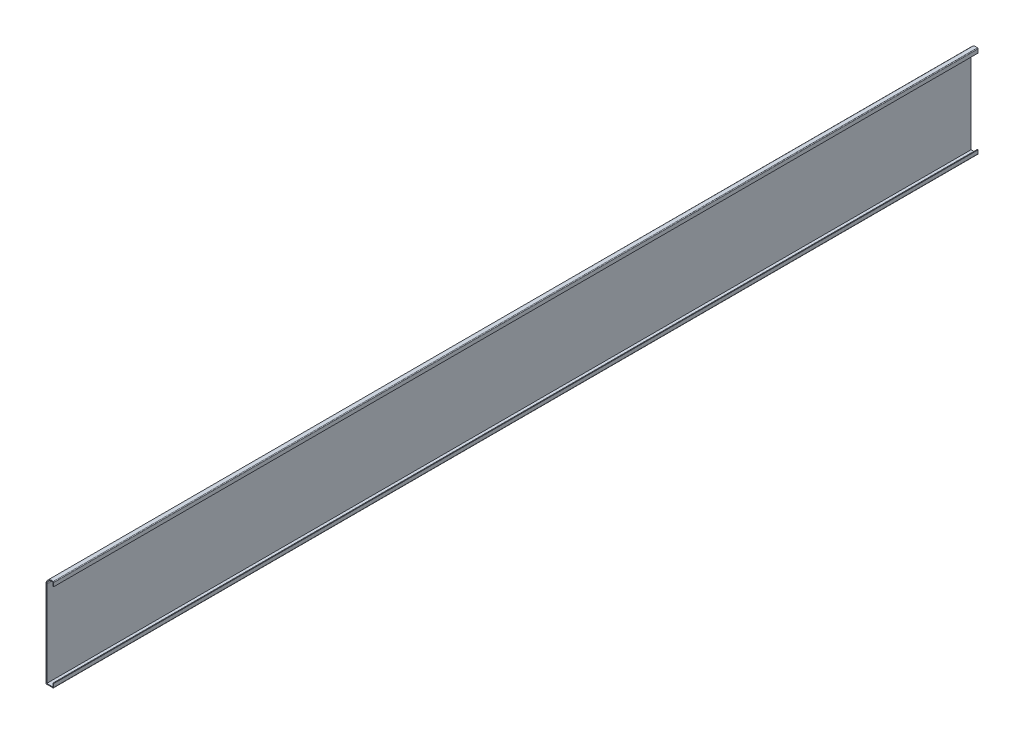
SolidWorks part; units mm, degrees
ref_plane "Front Plane" through (0, 0, 0) normal (0, 0, 1) x (1, 0, 0)
ref_plane "Top Plane" through (0, 0, 0) normal (0, 1, 0) x (1, 0, 0)
ref_plane "Right Plane" through (0, 0, 0) normal (1, 0, 0) x (0, 0, -1)
sketch "Sketch1" plane through (0, 0, 0) normal (0, 0, 1) x (1, 0, 0)
  line L0 (0, 6.858) -> (0, 0)
  line L1 (0, 0) -> (-12.7, 0)
  line L2 (-12.7, 0) -> (-12.7, 142.875)
  line L3 (0, 151.8553) -> (0, 144.9973)
  arc A0 (-12.7, 142.875) -> (0, 151.8553) centre (-3.175, 142.875) cw
  point P7 (0, 0)
  point P9 (0, 0)
  dimension "D5" = 9.525
  dimension "D1" = 152.4
  dimension "D2" = 6.858
  dimension "D3" = 6.858
  dimension "D4" = 12.7
extrude "Extrude-Thin1" add sketch "Sketch1" against normal blind 1524 thin
fillet "Fillet1" radius 1.27 3 edges at (-12.7, 0, -762) (0, 0, -762) (0, 151.8553, -762)
